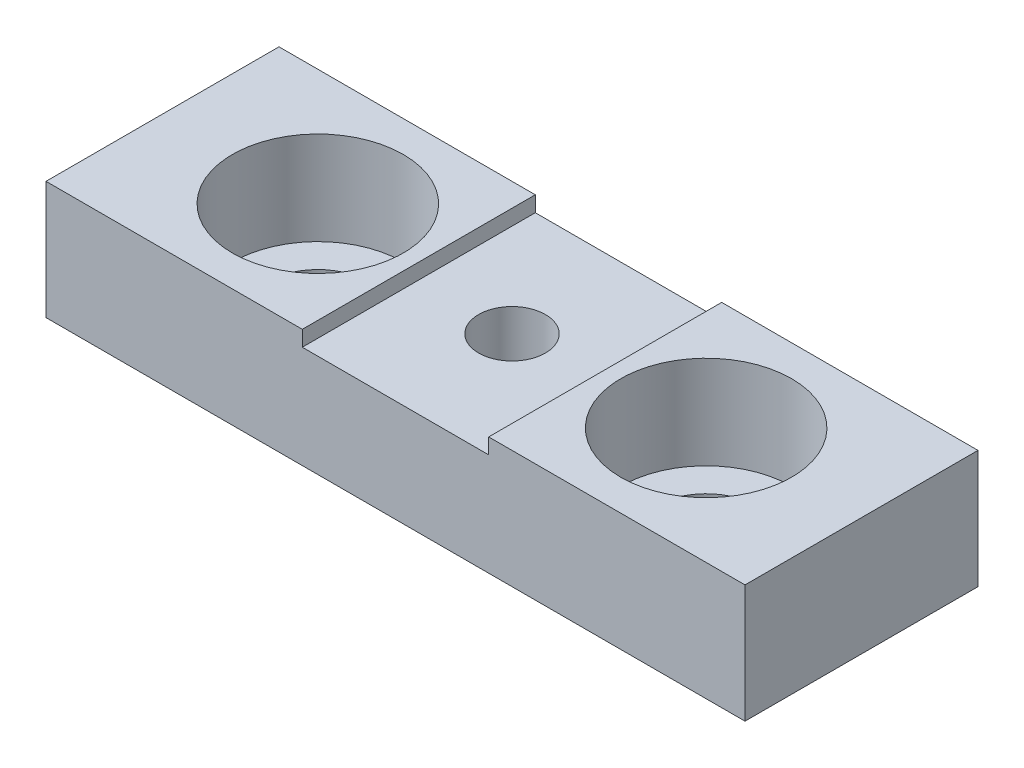
SolidWorks part; units mm, degrees
material "1060 Alloy"
ref_plane "Front" through (0, 0, 0) normal (0, 0, 1) x (1, 0, 0)
ref_plane "Top" through (0, 0, 0) normal (0, 1, 0) x (1, 0, 0)
ref_plane "Right" through (0, 0, 0) normal (1, 0, 0) x (0, 0, -1)
sketch "Sketch1" plane through (0, 0, 0) normal (0, 1, 0) x (1, 0, 0)
  line L1 (-22.5, -7.5) -> (22.5, -7.5)
  line L2 (-22.5, -7.5) -> (-22.5, 7.5)
  line L3 (-22.5, 7.5) -> (22.5, 7.5)
  line L4 (22.5, -7.5) -> (22.5, 7.5)
  line L5 (-22.5, -7.5) -> (22.5, 7.5) construction
  line L6 (-22.5, 7.5) -> (22.5, -7.5) construction
  circle A0 centre (0, 0) radius 2.15
  point P0 (0, 0)
  dimension "D3" = 4.3
  dimension "D1" = 45
  dimension "D2" = 15
extrude "Boss-Extrude1" add sketch "Sketch1" along normal blind 7.6
sketch "Sketch2" plane through (0, 7.6, 0) normal (0, 1, 0) x (1, 0, 0)
  line L0 (-23.5173, 0) -> (24.3282, 0) construction
  line L1 (-12.5, 9.6546) -> (-12.5, -10.2683) construction
  line L2 (12.5, 9.6546) -> (12.5, -10.2683) construction
  dimension "D1" = 12.5
  dimension "D2" = 12.5
hole_wizard "CBORE for M6 SHCS1" positions "Sketch3" profile "Sketch4" counterbore size "M6" standard "ANSI Metric" end condition through all
sketch "Sketch3" plane through (0, 7.6, 0) normal (0, 1, 0) x (1, 0, 0)
  line L0 (-23.5173, 0) -> (24.3282, 0) construction
  line L1 (22.5, -7.5) -> (22.5, 7.5) construction
  point P0 (-12.5, 0)
  point P4 (12.5, 0)
  dimension "D1" = 10
  dimension "D2" = 25
sketch "Sketch4" plane through (-12.5, 7.6, 0) normal (1, 0, 0) x (0, 0, 1)
  line L0 (0, 0) -> (0, 7.6)
  line L1 (0, 7.6) -> (3.3, 7.6)
  line L3 (3.3, 7.6) -> (3.3, 6)
  line L4 (3.3, 6) -> (5.5, 6)
  line L5 (5.5, 6) -> (5.5, 0)
  line L7 (5.5, 0) -> (0, 0)
  line L11 (0, -6.35) -> (0, 107.95) construction
  dimension "Thru Hole Dia." = 6.6
  dimension "Thru Hole Depth" = 7.6
  dimension "C'Bore Dia." = 11
  dimension "C'Bore Depth" = 6
sketch "Sketch5" plane through (0, 7.6, 0) normal (0, 1, 0) x (1, 0, 0)
  line L0 (22.5, 7.5) -> (-22.5, 7.5) construction
  line L1 (-6, 7.5) -> (6, 7.5)
  line L2 (-6, 7.5) -> (-6, -7.5)
  line L3 (-6, -7.5) -> (6, -7.5)
  line L4 (6, 7.5) -> (6, -7.5)
  line L5 (-22.5, -7.5) -> (22.5, -7.5) construction
  dimension "D1" = 12
  dimension "D2" = 6
extrude "Cut-Extrude2" cut sketch "Sketch5" against normal blind 1
